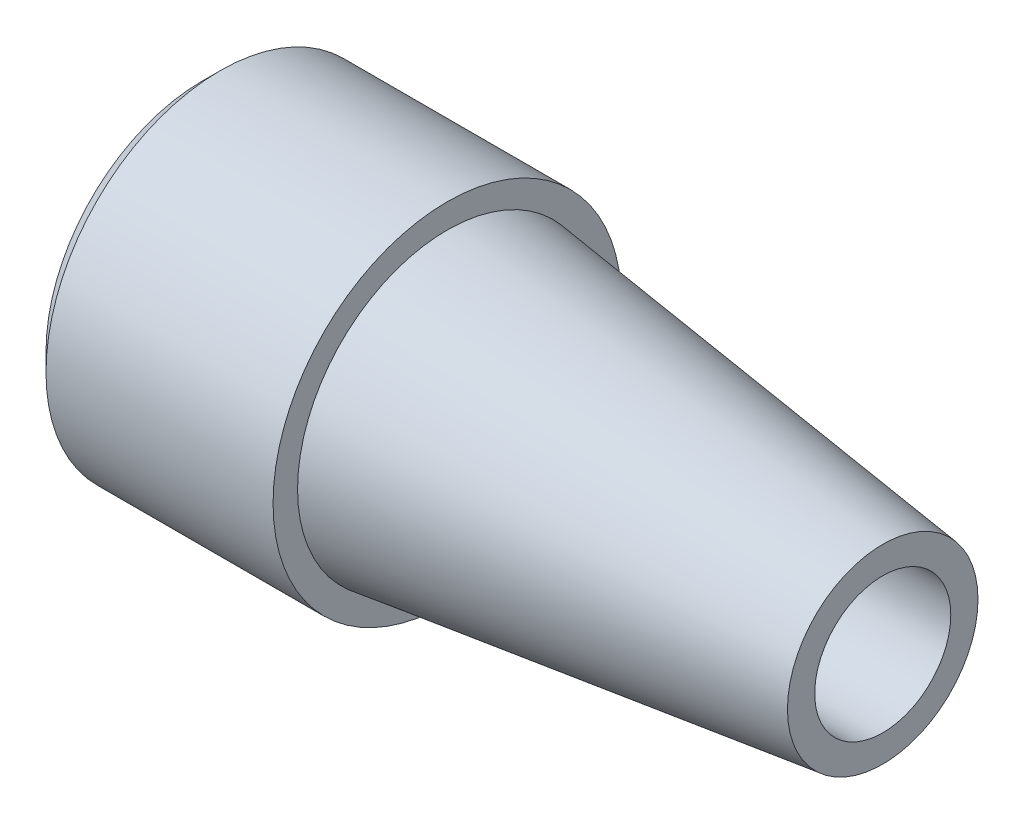
SolidWorks part; units mm, degrees
material "Сталь"
ref_plane "Спереди" through (0, 0, 0) normal (0, 0, 1) x (1, 0, 0)
ref_plane "Сверху" through (0, 0, 0) normal (0, 1, 0) x (1, 0, 0)
ref_plane "Справа" through (0, 0, 0) normal (1, 0, 0) x (0, 0, -1)
sketch "Эскиз1" plane through (0, 0, 0) normal (0, 0, 1) x (1, 0, 0)
  line L0 (0, 0) -> (-291.1314, 0) construction
  line L1 (-125, 27.5) -> (-80, 27.5)
  line L2 (-80, 27.5) -> (0, 17.5)
  line L3 (0, 17.5) -> (0, 12.5)
  line L4 (0, 12.5) -> (-77.2727, 12.5)
  line L5 (-125, 27.5) -> (-125, 25)
  line L6 (-125, 25) -> (-77.2727, 12.5)
  line L7 (-230, 52.5) -> (-230, -52.5) construction
  line L8 (-230, 52.5) -> (-125, 25) construction
  point P3 (-230, 52.5)
  dimension "D1" = 35
  dimension "D2" = 125
  dimension "D3" = 25
  dimension "D4" = 55
  dimension "D5" = 45
  dimension "D6" = 105
  dimension "D7" = 50
revolve "Повернуть1" add sketch "Эскиз1" angle 360 about L0
sketch "Эскиз4" plane through (-125, 0, 0) normal (-1, 0, 0) x (0, 0, 1)
  circle A0 centre (0, 0) radius 32
  circle A1 centre (0, 0) radius 27.5
  circle A2 centre (0, 0) radius 27.5 construction
  dimension "D1" = 64
extrude "Бобышка-Вытянуть1" add sketch "Эскиз4" against normal blind 45
cosmetic thread "Условное изображение резьбы1" parameters "D2"=57.425
chamfer "Фаска1" distance 3.2875 angle 45 1 edges at (-125, 0, 32)
